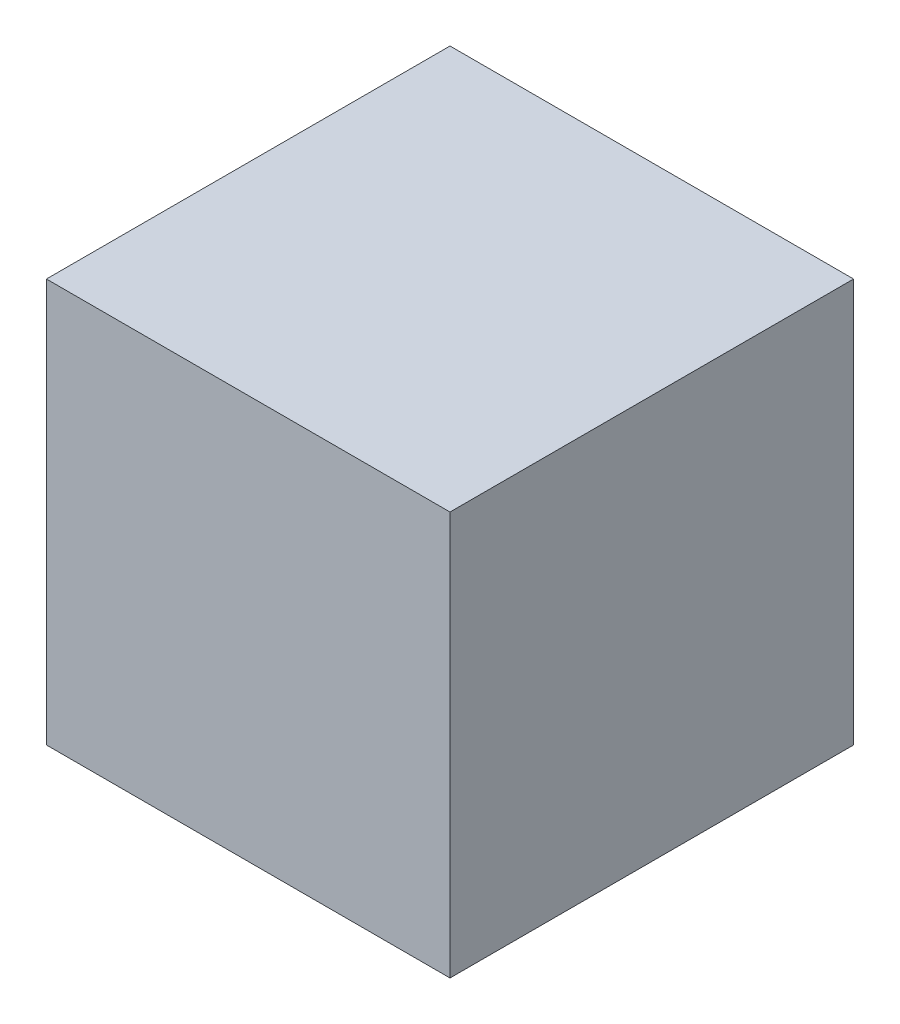
SolidWorks part; units mm, degrees
material "鎳"
ref_plane "前基準面" through (0, 0, 0) normal (0, 0, 1) x (1, 0, 0)
ref_plane "上基準面" through (0, 0, 0) normal (0, 1, 0) x (1, 0, 0)
ref_plane "右基準面" through (0, 0, 0) normal (1, 0, 0) x (0, 0, -1)
sketch "草圖1" plane through (0, 0, 0) normal (0, 0, 1) x (1, 0, 0)
  line L1 (-24, 24) -> (24, 24)
  line L2 (-24, 24) -> (-24, -24)
  line L3 (-24, -24) -> (24, -24)
  line L4 (24, 24) -> (24, -24)
  line L5 (-24, 24) -> (24, -24) construction
  line L6 (-24, -24) -> (24, 24) construction
  point P0 (0, 0)
  dimension "D1" = 48
  dimension "D2" = 48
extrude "填料-伸長1" add sketch "草圖1" along normal blind 48
sketch3d "URDF Reference"
  line L0 (0, 0, 0) -> (10, 0, 0) construction
  line L1 (0, 0, 0) -> (0, 0, -10) construction
  point P0 (0, 0, 0)
  point P1 (0, 0, 0)
